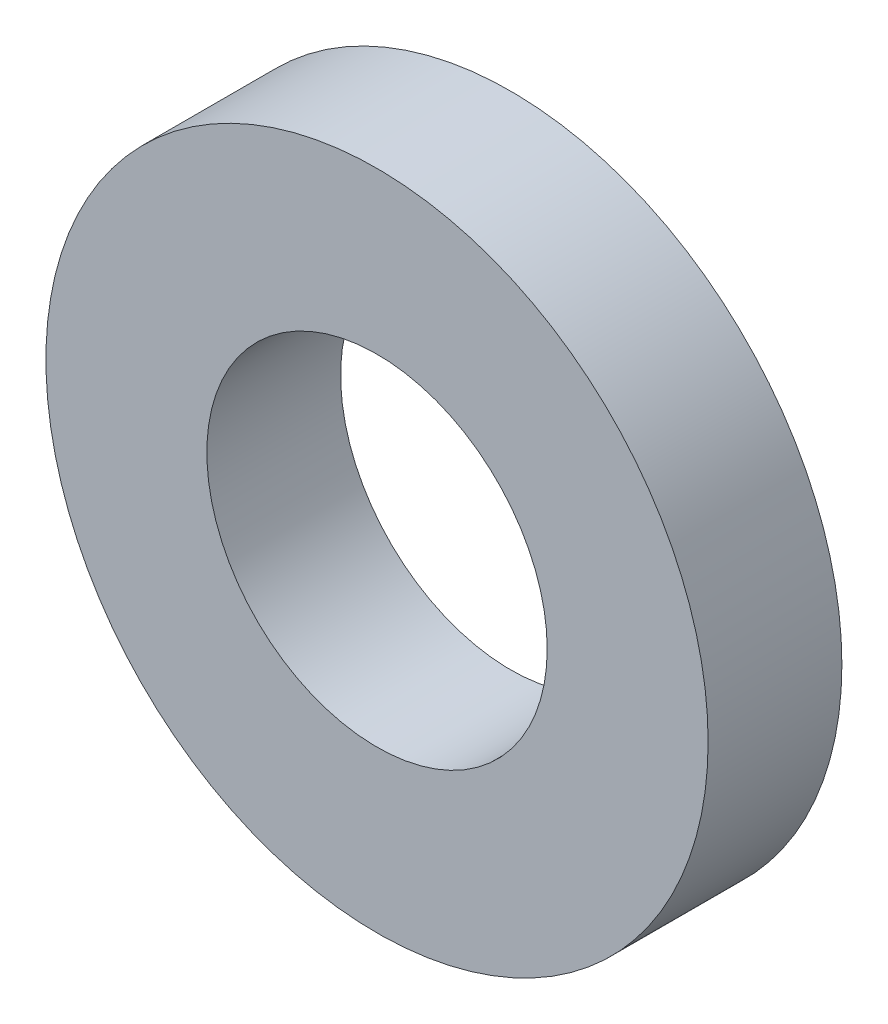
SolidWorks part; units mm, degrees
ref_plane "Front Plane" through (0, 0, 0) normal (0, 0, 1) x (1, 0, 0)
ref_plane "Top Plane" through (0, 0, 0) normal (0, 1, 0) x (1, 0, 0)
ref_plane "Right Plane" through (0, 0, 0) normal (1, 0, 0) x (0, 0, -1)
sketch "Sketch1" plane through (0, 0, 0) normal (0, 0, 1) x (1, 0, 0)
  circle A0 centre (0, 0) radius 3.2639
  circle A1 centre (0, 0) radius 6.35
  dimension "ID" = 6.5278
  dimension "OD" = 12.7
extrude "Extrude1" add sketch "Sketch1" against normal blind 2.5654
